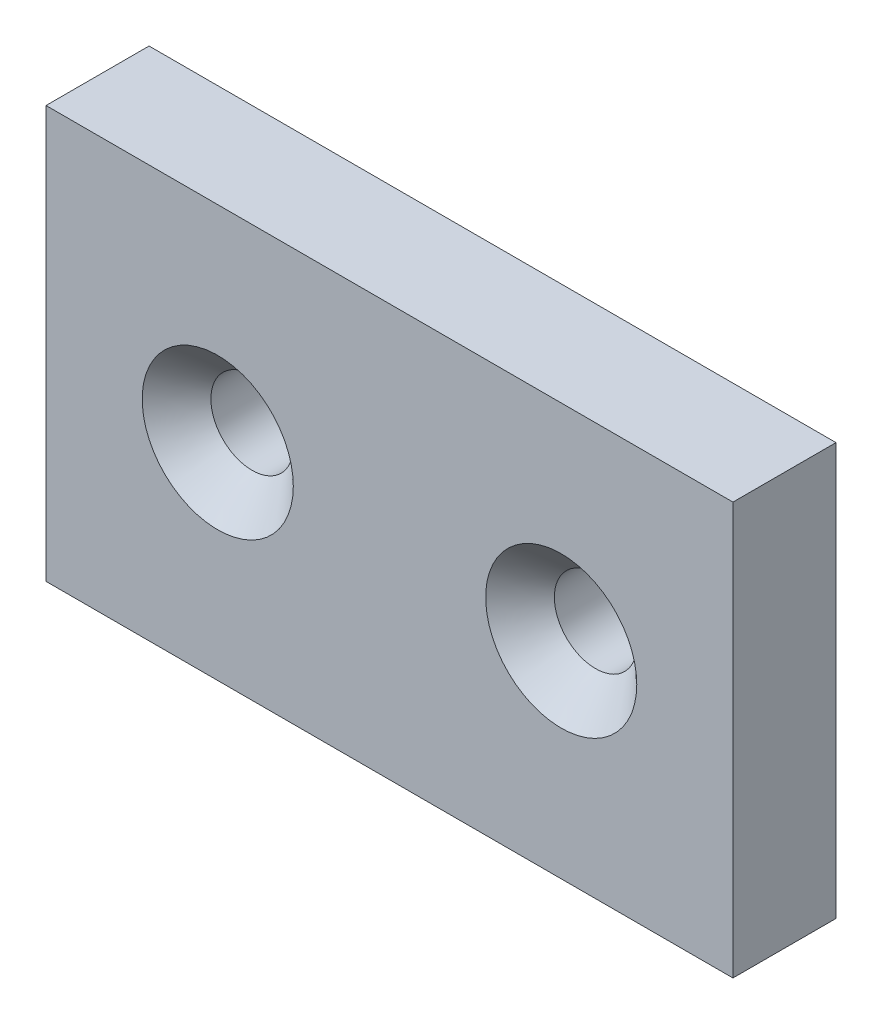
SolidWorks part; units mm, degrees
material "Gomma naturale"
ref_plane "Front" through (0, 0, 0) normal (0, 0, 1) x (1, 0, 0)
ref_plane "Top" through (0, 0, 0) normal (0, 1, 0) x (1, 0, 0)
ref_plane "Right" through (0, 0, 0) normal (1, 0, 0) x (0, 0, -1)
sketch "Schizzo1" plane through (0, 0, 0) normal (0, 0, 1) x (1, 0, 0)
  line L1 (0, 0) -> (20, 0)
  line L2 (0, 0) -> (0, 19.7)
  line L3 (0, 19.7) -> (20, 19.7)
  line L4 (20, 0) -> (20, 19.7)
  line L5 (0, 0) -> (20, 19.7) construction
  line L6 (0, 19.7) -> (20, 0) construction
  point P4 (10, 9.85)
extrude "Estrusione-Estrusione1" add sketch "Schizzo1" along normal blind 3
sketch "Schizzo2" plane through (0, 0, 3) normal (0, 0, 1) x (1, 0, 0)
  line L0 (0, 9.85) -> (5, 9.85)
  line L1 (0, 19.7) -> (0, 0) construction
  line L2 (5, 9.85) -> (15, 9.85)
  line L3 (15, 9.85) -> (20, 9.85)
  line L4 (20, 0) -> (20, 19.7) construction
hole_wizard "Foro svasato per Vite M2-2" positions "Schizzo5" profile "Schizzo6" countersink size "M2" standard "Ansi Metric" end condition through all
sketch "Schizzo5" plane through (0, 0, 3) normal (0, 0, 1) x (1, 0, 0)
  point P0 (5, 9.85)
  point P3 (15, 9.85)
sketch "Schizzo6" plane through (5, 9.85, 3) normal (1, 0, 0) x (0, -1, 0)
  line L0 (0, 0) -> (0, 3)
  line L1 (0, 3) -> (1.2, 3)
  line L2 (1.2, 3) -> (1.2, 1)
  line L3 (1.2, 1) -> (2.2, 0)
  line L5 (2.2, 0) -> (0, 0)
  line L6 (-1.2, 1) -> (-2.2, 0) construction
  line L11 (0, -6.35) -> (0, 107.95) construction
  dimension "Thru Hole Dia." = 2.4
  dimension "Thru Hole Depth" = 3
  dimension "Near C'Sink Dia." = 4.4
  dimension "Near C'Sink Angle" = 90
sketch "Schizzo7" plane through (0, 0, 0) normal (0, 0, -1) x (-1, 0, 0)
  line L1 (0, 19.7) -> (-20, 19.7)
  line L2 (0, 19.7) -> (0, 15.85)
  line L3 (0, 15.85) -> (-20, 15.85)
  line L4 (-20, 19.7) -> (-20, 15.85)
  line L5 (-20, 3.85) -> (0, 3.85)
  line L6 (-20, 3.85) -> (-20, 0)
  line L7 (-20, 0) -> (0, 0)
  line L8 (0, 3.85) -> (0, 0)
extrude "Taglio-Estrusione1" cut sketch "Schizzo7" against normal blind 10
